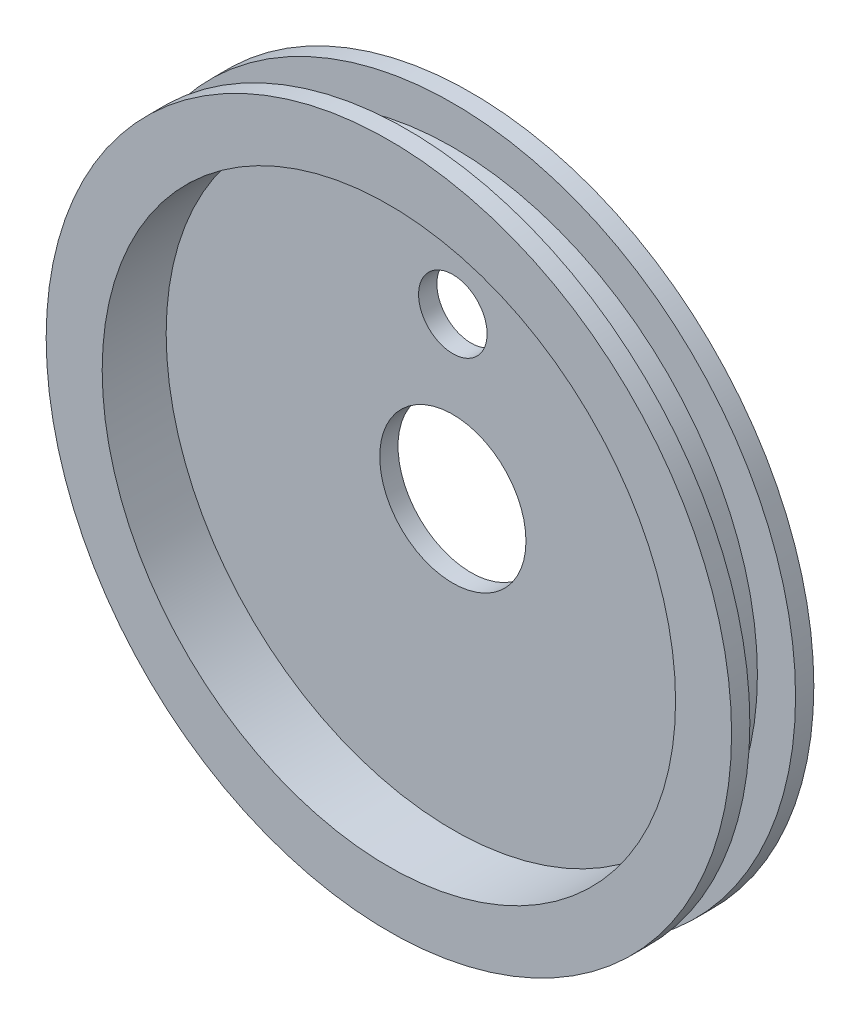
SolidWorks part; units mm, degrees
ref_plane "Front Plane" through (0, 0, 0) normal (0, 0, 1) x (1, 0, 0)
ref_plane "Top Plane" through (0, 0, 0) normal (0, 1, 0) x (1, 0, 0)
ref_plane "Right Plane" through (0, 0, 0) normal (1, 0, 0) x (0, 0, -1)
sketch "Sketch2" plane through (0, 0, 0) normal (1, 0, 0) x (0, 0, -1)
  line L0 (-6.35, 42.3253) -> (0, 42.3253)
  line L1 (-6.35, 42.3253) -> (-6.35, 47.625)
  line L2 (-6.35, 47.625) -> (-8.89, 47.625)
  line L3 (-8.89, 47.625) -> (-8.89, 39.8398)
  line L4 (0, 0) -> (0, 39.8398)
  line L5 (0, 39.8398) -> (-8.89, 39.8398)
  line L6 (0, 42.3253) -> (0, 47.625)
  line L7 (0, 47.625) -> (2.54, 47.625)
  line L8 (2.54, 47.625) -> (2.54, 0)
  line L9 (0, 0) -> (2.54, 0)
  dimension "D1" = 42.3253
  dimension "D2" = 6.35
  dimension "D3" = 47.625
  dimension "D4" = 2.54
revolve "Revolve1" add sketch "Sketch2" angle 360 about L9
sketch "Sketch3" plane through (0, 0, 0) normal (0, 0, 1) x (1, 0, 0)
  circle A0 centre (0, 0) radius 10.16
  dimension "D1" = 20.32
extrude "Cut-Extrude1" cut sketch "Sketch3" against normal blind 2.54
sketch "Sketch5" plane through (0, 0, 0) normal (0, 0, 1) x (1, 0, 0)
  circle A0 centre (0, 22.225) radius 4.7625
  dimension "D2" = 9.525
  dimension "D1" = 22.225
extrude "Cut-Extrude2" cut sketch "Sketch5" against normal blind 6.35
sketch "Sketch11" plane through (0, 0, 0) normal (0, 1, 0) x (1, 0, 0)
  circle A0 centre (0, -3.8704) radius 0.889
  dimension "D1" = 1.778
extrude "Cut-Extrude6" cut sketch "Sketch11" along normal blind 55.372
sketch "Sketch12" plane through (0, 0, -2.54) normal (0, 0, -1) x (-1, 0, 0)
  circle A0 centre (0, 0) radius 28.194
  circle A1 centre (0, 0) radius 26.924
  dimension "D1" = 56.388
  dimension "D2" = 53.848
extrude "Boss-Extrude1" add sketch "Sketch12" along normal blind 2.54
